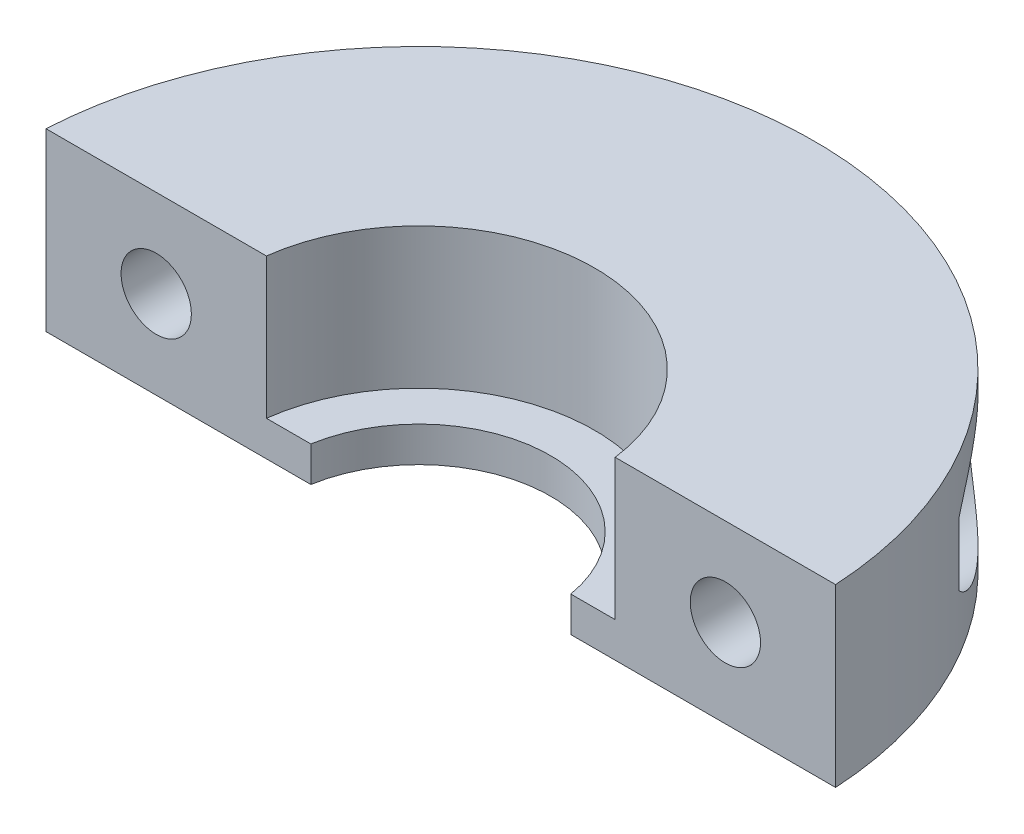
SolidWorks part; units mm, degrees
material "ABS"
ref_plane "Front Plane" through (0, 0, 0) normal (0, 0, 1) x (1, 0, 0)
ref_plane "Top Plane" through (0, 0, 0) normal (0, 1, 0) x (1, 0, 0)
ref_plane "Right Plane" through (0, 0, 0) normal (1, 0, 0) x (0, 0, -1)
sketch "Sketch1" plane through (0, 0, 0) normal (0, 1, 0) x (1, 0, 0)
  circle A0 centre (0, 0) radius 8
  circle A1 centre (0, 0) radius 18
  dimension "D1" = 16
  dimension "D2" = 10
extrude "Boss-Extrude1" add sketch "Sketch1" along normal blind 8
sketch "Sketch2" plane through (0, 0, 0) normal (0, 1, 0) x (1, 0, 0)
  circle A0 centre (0, 0) radius 8
  circle A1 centre (0, 0) radius 6
  dimension "D1" = 16
  dimension "D2" = 12
extrude "Boss-Extrude2" add sketch "Sketch2" along normal blind 1.6
sketch "Sketch3" plane through (0, 8, 0) normal (0, 1, 0) x (1, 0, 0)
  line L0 (-20, 1) -> (20, 1)
  line L1 (20, 1) -> (20, -19)
  line L2 (20, -19) -> (-20, -19)
  line L3 (-20, -19) -> (-20, 1)
  line L4 (0, 0) -> (0, 1) construction
  dimension "D1" = 20
  dimension "D2" = 1
  dimension "D3" = 40
extrude "Cut-Extrude1" cut sketch "Sketch3" against normal through all
sketch "Sketch5" plane through (0, 0, -1) normal (0, 0, 1) x (1, 0, 0)
  line L0 (-7.9373, 8) -> (-17.9722, 8) construction
  line L1 (-12.9547, 8) -> (-12.9547, 4) construction
  line L2 (-17.9722, 4) -> (-12.9547, 4) construction
  line L3 (-17.9722, 0) -> (-17.9722, 8) construction
  line L4 (12.9547, 8) -> (12.9547, 4) construction
  line L5 (17.9722, 8) -> (7.9373, 8) construction
  line L6 (12.9547, 4) -> (17.9722, 4) construction
  line L7 (17.9722, 8) -> (17.9722, 0) construction
  circle A0 centre (-12.9547, 4) radius 1.6
  circle A1 centre (12.9547, 4) radius 1.6
  dimension "D1" = 3.2
extrude "Cut-Extrude2" cut sketch "Sketch5" against normal up to next
sketch "Sketch6" plane through (0, 0, -1) normal (0, 0, 1) x (1, 0, 0)
  circle A0 centre (-12.9547, 4) radius 3
  circle A1 centre (12.9547, 4) radius 3
  dimension "D1" = 6
extrude "Cut-Extrude3" cut sketch "Sketch6" against normal up to next from offset 8
